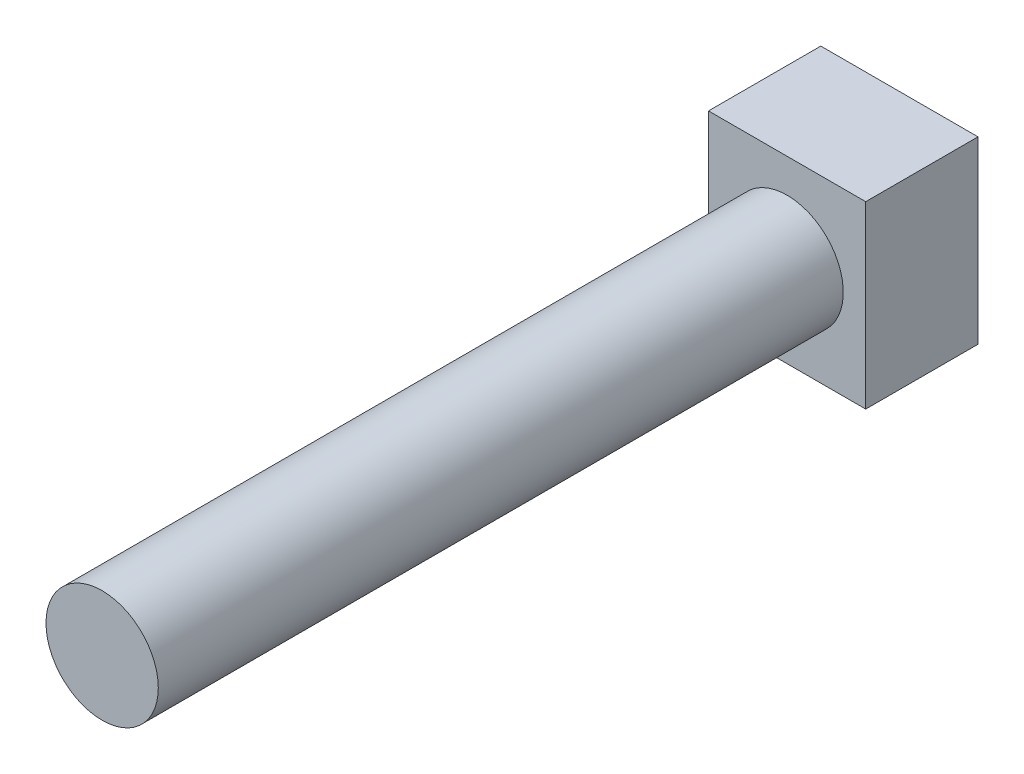
SolidWorks part; units mm, degrees
ref_plane "Front" through (0, 0, 0) normal (0, 0, 1) x (1, 0, 0)
ref_plane "Top" through (0, 0, 0) normal (0, 1, 0) x (1, 0, 0)
ref_plane "Right" through (0, 0, 0) normal (1, 0, 0) x (0, 0, -1)
sketch "Sketch2" plane through (0, 0, 0) normal (0, 0, 1) x (1, 0, 0)
  circle A0 centre (0, 0) radius 2.5
  dimension "D1" = 5
extrude "Boss-Extrude1" add sketch "Sketch2" along normal blind 35.5 contours A0
sketch "Sketch4" plane through (0, 0, 0) normal (0, 0, -1) x (-1, 0, 0)
  line L1 (-3.5, 4) -> (3.5, 4)
  line L2 (-3.5, 4) -> (-3.5, -4)
  line L3 (-3.5, -4) -> (3.5, -4)
  line L4 (3.5, 4) -> (3.5, -4)
  line L5 (-3.5, 4) -> (3.5, -4) construction
  line L6 (-3.5, -4) -> (3.5, 4) construction
  point P0 (0, 0)
  dimension "D1" = 7
  dimension "D2" = 8
extrude "Boss-Extrude4" add sketch "Sketch4" against normal blind 5
sketch "Sketch5" plane through (0, 0, 0) normal (0, 0, -1) x (-1, 0, 0)
  line L0 (0, 0) -> (0, 2.2461)
  line L1 (0, 0) -> (1.9792, 0)
  line L2 (0, 0) -> (-1.3343, 0)
  line L3 (0, 0) -> (0, -1.1786)
